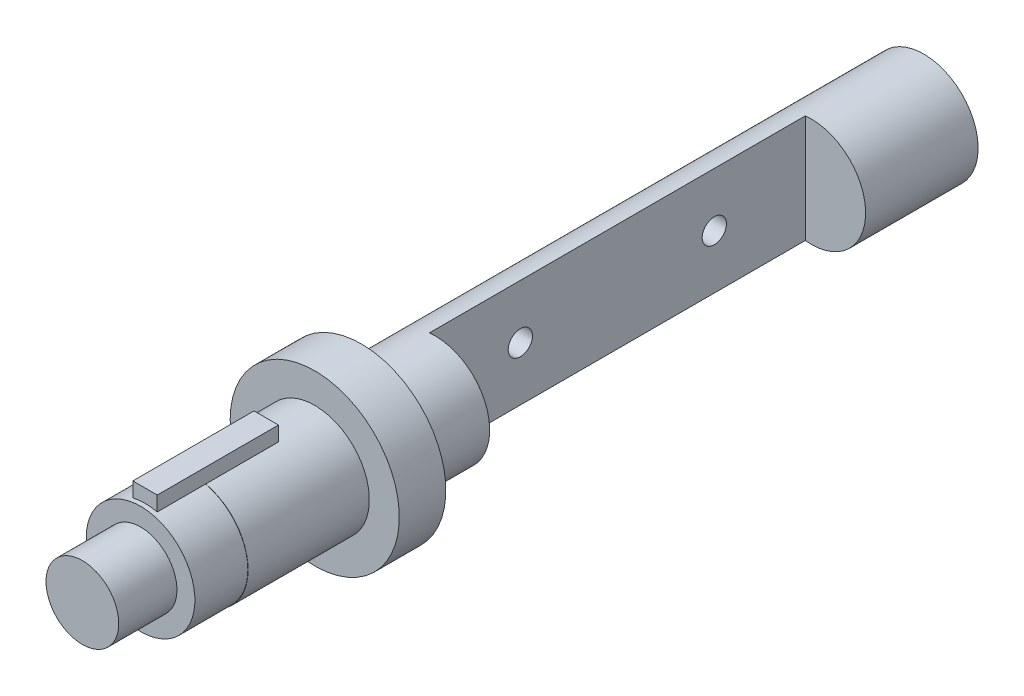
SolidWorks part; units mm, degrees
ref_plane "Front Plane" through (0, 0, 0) normal (0, 0, 1) x (1, 0, 0)
ref_plane "Top Plane" through (0, 0, 0) normal (0, 1, 0) x (1, 0, 0)
ref_plane "Right Plane" through (0, 0, 0) normal (1, 0, 0) x (0, 0, -1)
sketch "Sketch1" plane through (0, 0, 0) normal (0, 1, 0) x (1, 0, 0)
  line L0 (0, 0) -> (0, -636.3515) construction
  line L1 (0, 0) -> (28, 0)
  line L2 (28, 0) -> (28, -290)
  line L3 (28, -290) -> (43.6, -290)
  line L4 (43.6, -290) -> (43.6, -314)
  line L5 (43.6, -314) -> (28, -314)
  line L6 (28, -314) -> (28, -403.8)
  line L7 (28, -403.8) -> (18.75, -403.8)
  line L8 (18.75, -403.8) -> (18.75, -433.8)
  line L9 (18.75, -433.8) -> (0, -433.8)
  line L10 (0, -433.8) -> (0, 0)
  dimension "D1" = 433.8
  dimension "D2" = 28
  dimension "D3" = 43.6
  dimension "D4" = 28
  dimension "D5" = 18.75
  dimension "D6" = 290
  dimension "D7" = 24
  dimension "D8" = 89.8
revolve "Revolve1" add sketch "Sketch1" angle 360 about L0
sketch "Sketch2" plane through (0, 0, 314) normal (0, 0, 1) x (1, 0, 0)
  circle A0 centre (0, 0) radius 28.15
  dimension "D1" = 56.3
extrude "Boss-Extrude1" add sketch "Sketch2" along normal blind 62.5
sketch "Sketch3" plane through (0, 0, 314) normal (0, 0, 1) x (1, 0, 0)
  line L0 (-6.3, 35) -> (6.3, 35)
  line L1 (-6.3, 35) -> (-6.3, 27.436)
  line L2 (6.3, 35) -> (6.3, 27.436)
  arc A3 (6.3, 27.436) -> (-6.3, 27.436) centre (0, 0) ccw
  dimension "D4" = 56.3
  dimension "D1" = 12.6
  dimension "D2" = 6.3
  dimension "D3" = 35
extrude "Boss-Extrude2" add sketch "Sketch3" along normal blind 62.5 from offset 25
sketch "Sketch5" plane through (0, 0, 0) normal (0, 1, 0) x (1, 0, 0)
  line L0 (28, -290) -> (28, 0) construction
  line L1 (28, -58) -> (-3.1, -58)
  line L2 (28, -58) -> (28, -251.8)
  line L3 (28, -251.8) -> (-3.1, -251.8)
  line L4 (-3.1, -58) -> (-3.1, -251.8)
  line L5 (28, 0) -> (-28, 0) construction
  dimension "D1" = 193.8
  dimension "D2" = 58
  dimension "D3" = 31.1
extrude "Cut-Extrude1" cut sketch "Sketch5" against normal through all and the other way through all
sketch "Sketch6" plane through (-3.1, 0, 0) normal (1, 0, 0) x (0, 0, -1)
  line L0 (-58, -27.8279) -> (-58, 27.8279) construction
  circle A0 centre (-204.9, 0) radius 6.25
  circle A1 centre (-104.9, 0) radius 6.25
  dimension "D1" = 12.5
  dimension "D2" = 12.5
  dimension "D3" = 100
  dimension "D4" = 46.9
extrude "Cut-Extrude2" cut sketch "Sketch6" against normal through all
